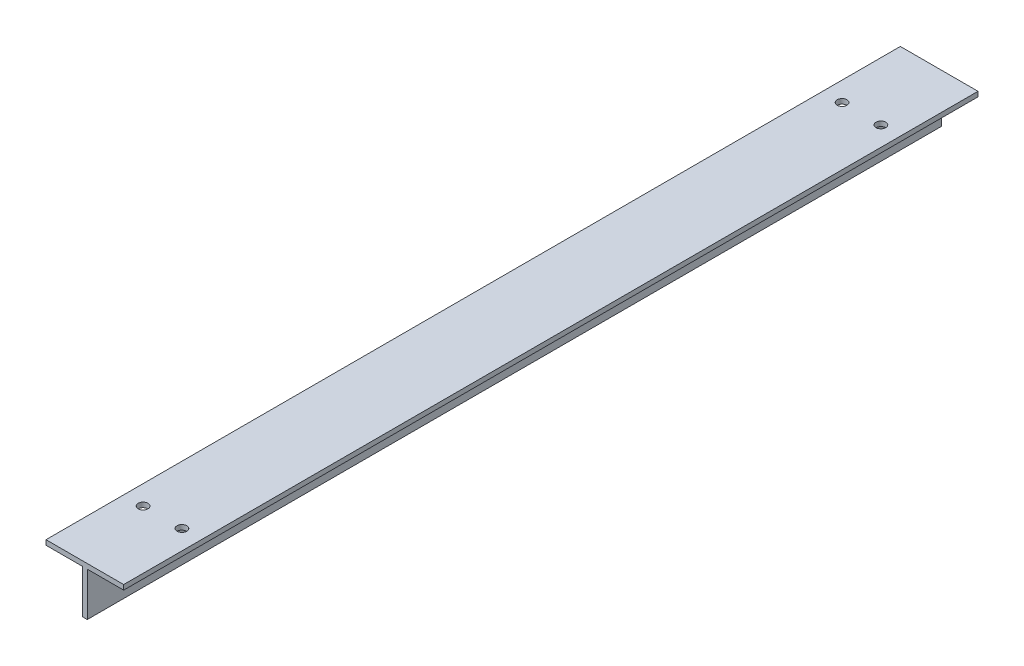
SolidWorks part; units mm, degrees
ref_plane "Front" through (0, 0, 0) normal (0, 0, 1) x (1, 0, 0)
ref_plane "Top" through (0, 0, 0) normal (0, 1, 0) x (1, 0, 0)
ref_plane "Right" through (0, 0, 0) normal (1, 0, 0) x (0, 0, -1)
sketch "Sketch1" plane through (0, 0, 0) normal (0, 0, 1) x (1, 0, 0)
  line L0 (-25.4, 31.75) -> (-25.4, 28.575)
  line L1 (-25.4, 28.575) -> (-1.5875, 28.575)
  line L2 (-1.5875, 28.575) -> (-1.5875, 0)
  line L3 (-1.5875, 0) -> (1.5875, 0)
  line L4 (1.5875, 0) -> (1.5875, 28.575)
  line L5 (1.5875, 28.575) -> (25.4, 28.575)
  line L6 (25.4, 28.575) -> (25.4, 31.75)
  line L7 (25.4, 31.75) -> (-25.4, 31.75)
  dimension "Thickness" = 3.175
  dimension "Width" = 50.8
  dimension "Height" = 31.75
extrude "Boss-Extrude1" add sketch "Sketch1" along normal mid plane 558.8
sketch "Sketch2" plane through (1.5875, 0, 0) normal (1, 0, 0) x (0, 0, -1)
  line L0 (0, 15.875) -> (0, 147.1907) construction
  line L1 (-279.4, 28.575) -> (279.4, 28.575) construction
  line L3 (-279.4, 28.575) -> (279.4, 28.575) construction
  circle A0 centre (-254, 15.875) radius 3.5
  circle A1 centre (254, 15.875) radius 3.5
  dimension "D1" = 7
  dimension "D3" = 12.7
  dimension "D2" = 12.7
  dimension "D4" = 254
extrude "Cut-Extrude1" cut sketch "Sketch2" against normal through all
sketch "Sketch3" plane through (0, 31.75, 0) normal (0, 1, 0) x (1, 0, 0)
  line L0 (0, -279.4) -> (0, 279.4) construction
  line L2 (25.4, 0) -> (-25.4, 0) construction
  line L3 (25.4, -279.4) -> (25.4, 279.4) construction
  line L4 (-25.4, -279.4) -> (-25.4, 279.4) construction
  line L5 (25.4, -279.4) -> (-25.4, -279.4) construction
  line L6 (25.4, 279.4) -> (-25.4, 279.4) construction
  circle A0 centre (-12.7, 228.6) radius 3.175
  circle A1 centre (12.7, 228.6) radius 3.175
  circle A2 centre (12.7, -228.6) radius 3.175
  circle A3 centre (-12.7, -228.6) radius 3.175
  dimension "D1" = 6.35
  dimension "D2" = 228.6
  dimension "D3" = 12.7
extrude "Cut-Extrude2" cut sketch "Sketch3" against normal through all
